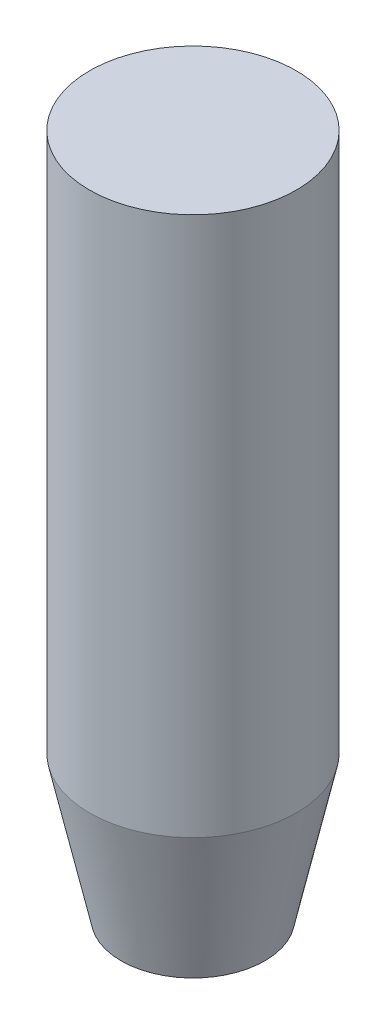
SolidWorks part; units mm, degrees
material "6061-T6 (SS)"
ref_plane "Front Plane" through (0, 0, 0) normal (0, 0, 1) x (1, 0, 0)
ref_plane "Top Plane" through (0, 0, 0) normal (0, 1, 0) x (1, 0, 0)
ref_plane "Right Plane" through (0, 0, 0) normal (1, 0, 0) x (0, 0, -1)
sketch "Sketch1" plane through (0, 0, 0) normal (0, 1, 0) x (1, 0, 0)
  circle A0 centre (0, 0) radius 18.2562
  dimension "D1" = 36.5125
extrude "Boss-Extrude1" add sketch "Sketch1" along normal blind 120.65
chamfer "Chamfer1" distance 5.5562 distance2 25.4 1 edges at (0, 0, 18.2562)
